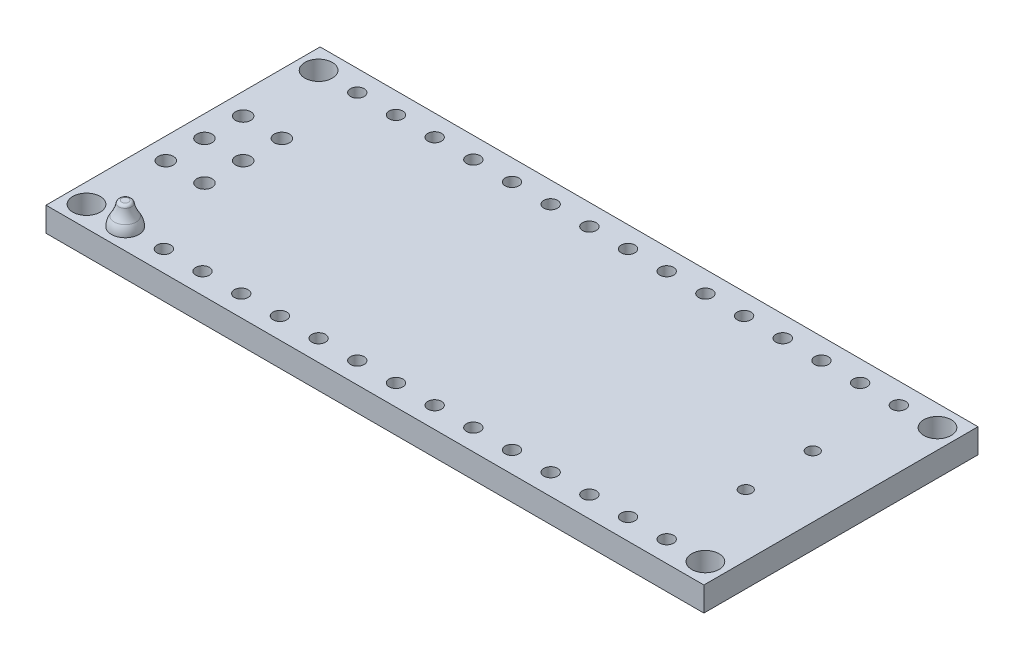
SolidWorks part; units mm, degrees
material "E-Glass Fiber"
ref_plane "Front Plane" through (0, 0, 0) normal (0, 0, 1) x (1, 0, 0)
ref_plane "Top Plane" through (0, 0, 0) normal (0, 1, 0) x (1, 0, 0)
ref_plane "Right Plane" through (0, 0, 0) normal (1, 0, 0) x (0, 0, -1)
sketch "Sketch1" plane through (0, 0, 0) normal (0, 1, 0) x (1, 0, 0)
  line L0 (0, 7.62) -> (-3.82, 7.62) construction
  line L1 (-3.82, 16.62) -> (39.38, 16.62)
  line L2 (-3.82, 16.62) -> (-3.82, -1.38)
  line L3 (-3.82, -1.38) -> (39.38, -1.38)
  line L4 (39.38, 16.62) -> (39.38, -1.38)
  line L5 (0, 0) -> (35.56, 0) construction
  line L6 (0, 0) -> (0, 15.24) construction
  line L7 (0, 15.24) -> (35.56, 15.24) construction
  line L8 (35.56, 0) -> (35.56, 15.24) construction
  line L10 (35.56, 7.62) -> (39.38, 7.62) construction
  dimension "D1" = 43.2
  dimension "D2" = 18
  dimension "D3" = 15.24
  dimension "D4" = 35.56
extrude "Boss-Extrude2" add sketch "Sketch1" along normal blind 1.6
sketch "Sketch2" plane through (0, 0, 0) normal (0, 1, 0) x (1, 0, 0)
  line L0 (0, -0.88) -> (0, 0.88) construction
  line L2 (-0.88, 0) -> (0.88, 0) construction
  circle A0 centre (0, 0) radius 0.45
  circle A1 centre (0, 15.24) radius 0.45
  dimension "D1" = 0.9
  dimension "D2" = 15.24
extrude "Cut-Extrude2" cut sketch "Sketch2" along normal blind 1.6
pattern_linear "LPattern1" count 15 spacing 2.54 along (1, 0, 0) of "Cut-Extrude2"
sketch "Sketch3" plane through (0, 0, 0) normal (0, 1, 0) x (1, 0, 0)
  line L1 (-0.88, 0) -> (0.88, 0) construction
  line L2 (0, -0.88) -> (0, 0.88) construction
  circle A0 centre (0.127, 10.16) radius 0.5
  circle A1 centre (-2.413, 10.16) radius 0.5
  circle A2 centre (-2.413, 7.62) radius 0.5
  circle A3 centre (-2.413, 5.08) radius 0.5
  circle A4 centre (0.127, 5.08) radius 0.5
  circle A5 centre (0.127, 7.62) radius 0.5
  dimension "D1" = 1
  dimension "D5" = 7.62
  dimension "D2" = 2.54
  dimension "D3" = 2.54
  dimension "D4" = 2.54
  dimension "D6" = 2.54
  dimension "D7" = 0.127
extrude "Cut-Extrude4" cut sketch "Sketch3" along normal blind 1.6
sketch "Sketch4" plane through (0, 0, 0) normal (0, 1, 0) x (1, 0, 0)
  line L0 (-0.88, 0) -> (0.88, 0) construction
  line L1 (0, -0.88) -> (0, 0.88) construction
  circle A0 centre (38.1, 15.24) radius 0.9
  circle A1 centre (38.1, 0) radius 0.9
  circle A2 centre (-2.54, 0) radius 0.9
  circle A3 centre (-2.54, 15.24) radius 0.9
  dimension "D3" = 1.8
  dimension "D1" = 40.64
  dimension "D2" = 2.54
  dimension "D4" = 15.24
  dimension "D5" = 15.24
extrude "Cut-Extrude5" cut sketch "Sketch4" along normal blind 1.6
sketch "Sketch5" plane through (0, 1.6, 0) normal (0, 1, 0) x (1, 0, 0)
  circle A0 centre (38.1, 15.24) radius 0.9
  circle A1 centre (38.1, 15.24) radius 1.275
  circle A2 centre (38.1, 15.24) radius 0.9 construction
  circle A3 centre (38.1, 0) radius 0.9
  circle A4 centre (38.1, 0) radius 0.9 construction
  circle A5 centre (38.1, 0) radius 1.275
  circle A6 centre (-2.54, 15.24) radius 0.9
  circle A7 centre (-2.54, 15.24) radius 1.275
  circle A8 centre (-2.54, 0) radius 0.9
  circle A9 centre (-2.54, 0) radius 1.275
  circle A10 centre (-2.54, 15.24) radius 0.9 construction
  circle A11 centre (-2.54, 0) radius 0.9 construction
  dimension "D1" = 2.55
extrude "Boss-Extrude3" [suppressed] add sketch "Sketch5" along normal blind 0.1
sketch "Sketch6" plane through (0, 0, 0) normal (1, 0, 0) x (0, 0, -1)
  line L0 (0, 1.6) -> (0.9, 1.6)
  line L1 (-1.38, 1.6) -> (16.62, 1.6) construction
  line L2 (0.2252, 3.1) -> (0, 3.1)
  line L3 (0, 2.53) -> (0, -2.53) construction
  line L4 (0, 3.1) -> (0, 1.6)
  line L5 (0, 1.3722) -> (0, 3.4408) construction
  arc A0 (0.9, 1.6) -> (0.7139, 2.2122) centre (-0.2, 1.6) ccw
  arc A1 (0.7139, 2.2122) -> (0.4221, 2.9352) centre (2.2924, 3.2697) cw
  arc A2 (0.4221, 2.9352) -> (0.2252, 3.1) centre (0.2252, 2.9) ccw
  point P16 (0.4, 3.1)
  dimension "D4" = 1.1
  dimension "D5" = 1.9
  dimension "D6" = 0.2
  dimension "D1" = 1.5
  dimension "D2" = 0.8
  dimension "D3" = 1.8
revolve "Revolve1" add sketch "Sketch6" angle 360 about L5
pattern_linear "LPattern2" [suppressed] count 2 spacing 15.24 count 15 spacing 2.54
ref_plane "Plane3" through (0, 0, -5.08) normal (0, 0, 1) x (1, 0, 0)
sketch "Sketch7" plane through (0, 0, -5.08) normal (0, 0, 1) x (1, 0, 0)
  line L0 (0.127, 3.889) -> (0.127, -2.5597) construction
  line L2 (0, -1.705) -> (0, 1.705) construction
  line L3 (0.127, 0) -> (1.027, 0)
  line L4 (9.9, 0) -> (-9.9, 0) construction
  line L5 (0.127, 0) -> (0.127, -1.5)
  line L6 (0.127, -1.5) -> (0.3395, -1.5)
  arc A0 (0.538, -1.325) -> (0.807, -0.66) centre (1.927, -1.5) cw
  arc A1 (0.807, -0.66) -> (1.027, 0) centre (-0.073, 0) ccw
  arc A2 (0.3395, -1.5) -> (0.538, -1.325) centre (0.3395, -1.3) ccw
  point P16 (0.527, -1.5)
  dimension "D5" = 1.1
  dimension "D6" = 0.2
  dimension "D1" = 0.127
  dimension "D2" = 1.5
  dimension "D3" = 0.8
  dimension "D4" = 1.8
revolve "Revolve2" add sketch "Sketch7" angle 360 about L0
pattern_linear "LPattern3" count 2 spacing 2.54 along (-1, 0, 0) count 3 spacing 2.54 along (0, 0, -1) of "Revolve2"
sketch "Sketch8" plane through (0, 0, 0) normal (0, -1, 0) x (1, 0, 0)
  circle A0 centre (38.1, 0) radius 0.9
  circle A1 centre (38.1, 0) radius 1.275
  circle A2 centre (38.1, -15.24) radius 1.275
  circle A3 centre (38.1, -15.24) radius 0.9
  circle A4 centre (38.1, -15.24) radius 0.9 construction
  circle A5 centre (38.1, 0) radius 0.9 construction
  circle A6 centre (-2.54, 0) radius 0.9
  circle A7 centre (-2.54, 0) radius 1.275
  circle A8 centre (-2.54, -15.24) radius 0.9
  circle A9 centre (-2.54, -15.24) radius 1.275
  circle A10 centre (-2.54, 0) radius 0.9 construction
  circle A11 centre (-2.54, -15.24) radius 0.9 construction
  dimension "D1" = 2.55
extrude "Boss-Extrude4" [suppressed] add sketch "Sketch8" along normal blind 0.1
sketch "Sketch9" plane through (0, 0, 0) normal (0, 1, 0) x (1, 0, 0)
  line L0 (-2.53, 0) -> (2.53, 0) construction
  line L1 (39.38, -1.38) -> (39.38, 16.62) construction
  circle A0 centre (35.33, 5.42) radius 0.4
  circle A1 centre (35.33, 9.82) radius 0.4
  dimension "D1" = 0.8
  dimension "D2" = 4.4
  dimension "D3" = 5.42
  dimension "D4" = 4.05
extrude "Cut-Extrude6" cut sketch "Sketch9" along normal blind 10
